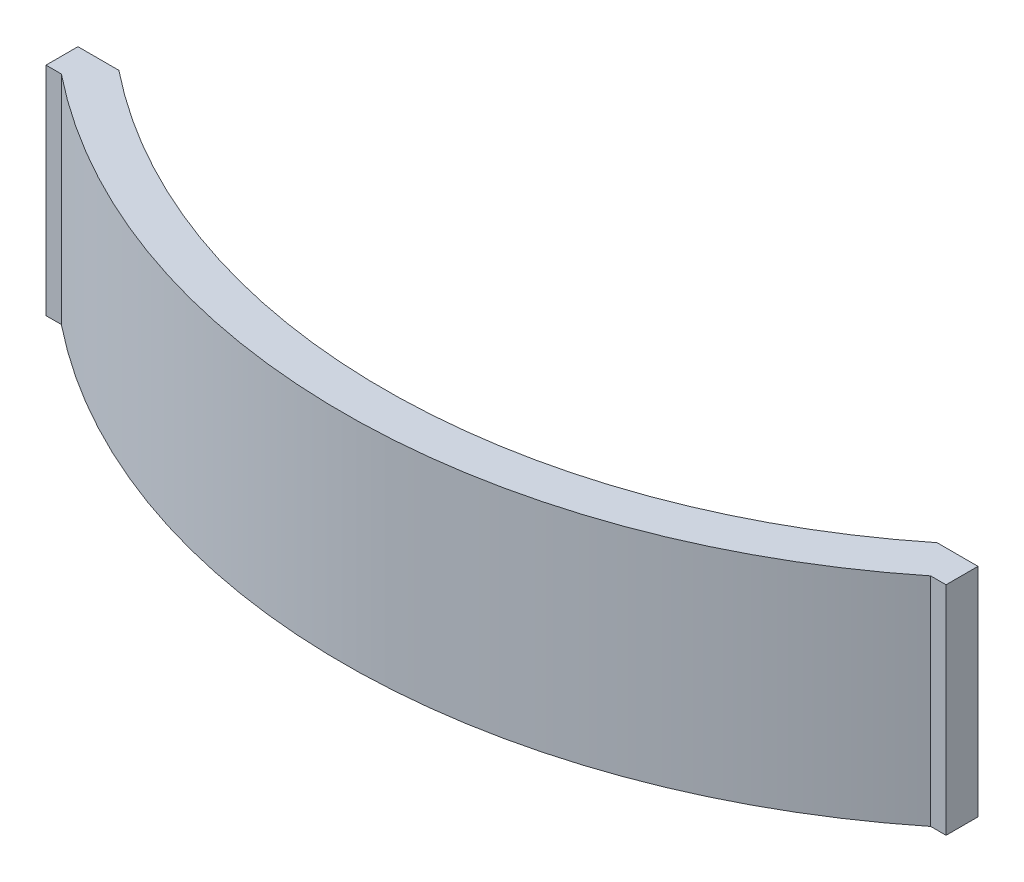
SolidWorks part; units mm, degrees
material "Silicon Rubber"
ref_plane "Front Plane" through (0, 0, 0) normal (0, 0, 1) x (1, 0, 0)
ref_plane "Top Plane" through (0, 0, 0) normal (0, 1, 0) x (1, 0, 0)
ref_plane "Right Plane" through (0, 0, 0) normal (1, 0, 0) x (0, 0, -1)
sketch "Sketch2" plane through (0, 0, 0) normal (0, 1, 0) x (1, 0, 0)
  line L0 (-31.75, -39.6557) -> (31.75, -39.6557) construction
  line L2 (-34.9256, -39.6557) -> (-31.75, -39.6557)
  line L5 (-39.7801, -36.4807) -> (39.7801, -36.4807) construction
  line L9 (-33.7344, -42.1342) -> (-34.9256, -42.1342)
  line L10 (-34.9256, -39.6557) -> (-34.9256, -42.1342)
  line L11 (0, -39.6557) -> (0, -32.0357) construction
  line L12 (33.7344, -42.1342) -> (34.9256, -42.1342)
  line L13 (34.9256, -42.1342) -> (34.9256, -39.6557)
  line L14 (34.9256, -39.6557) -> (31.75, -39.6557)
  arc A0 (-31.75, -39.6557) -> (31.75, -39.6557) centre (0, 0) ccw
  arc A2 (-33.7344, -42.1342) -> (33.7344, -42.1342) centre (0, 0) ccw
  arc A3 (-39.7801, -36.4807) -> (39.7801, -36.4807) centre (0, 0) ccw construction
  dimension "D1" = 101.6
  dimension "D2" = 63.5
  dimension "D4" = 2.4785
  dimension "D5" = 1.1913
  dimension "D6" = 7.62
  dimension "D7" = 1.1913
  dimension "D8" = 2.4785
  dimension "D9" = 3.1756
  dimension "D3" = 3.175
extrude "Boss-Extrude1" add sketch "Sketch2" along normal blind 16.8402 contours A0 L14 L13 L12 A2 L9 L10 L2
